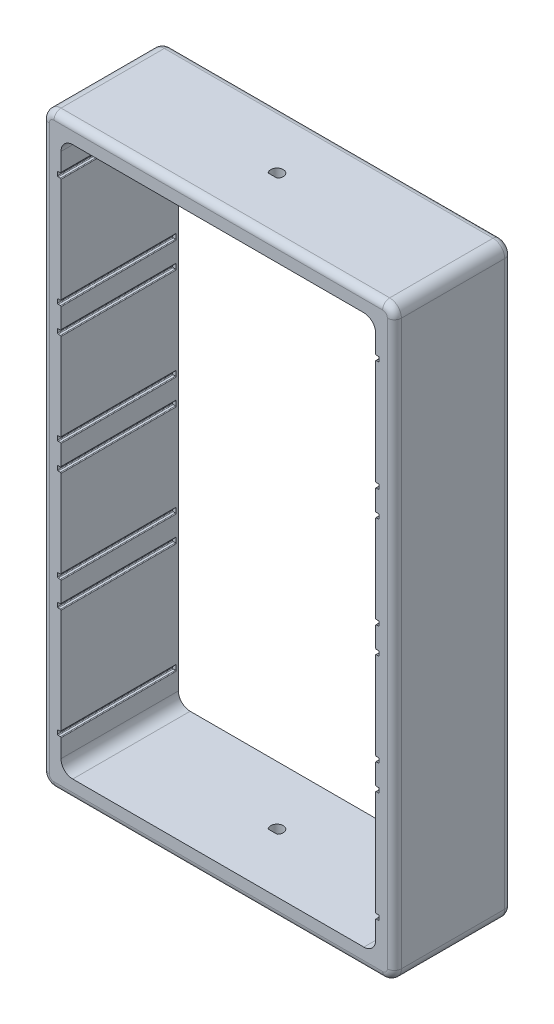
SolidWorks part; units mm, degrees
other "Markup1"
sketch "Sketch8" plane through (101.6, 152.4, 25.4) normal (0.0906, 0.2617, 0.9609) x (0.9959, -0.0171, -0.0892)
ref_plane "Front Plane" through (0, 0, 0) normal (0, 0, 1) x (1, 0, 0)
ref_plane "Top Plane" through (0, 0, 0) normal (0, 1, 0) x (1, 0, 0)
ref_plane "Right Plane" through (0, 0, 0) normal (1, 0, 0) x (0, 0, -1)
sketch "Sketch1" plane through (0, 0, 0) normal (0, 0, 1) x (1, 0, 0)
  line L1 (0, 0) -> (150, 0)
  line L2 (0, 0) -> (0, 250)
  line L3 (0, 250) -> (150, 250)
  line L4 (150, 0) -> (150, 250)
  dimension "D1" = 250
  dimension "D2" = 150
extrude "Boss-Extrude1" add sketch "Sketch1" along normal mid plane 50
sketch "Sketch2" plane through (0, 0, 25) normal (0, 0, 1) x (1, 0, 0)
  line L7 (150, 0) -> (150, 250) construction
  line L8 (8, 242) -> (142, 242)
  line L9 (8, 242) -> (8, 8)
  line L10 (8, 8) -> (142, 8)
  line L11 (142, 242) -> (142, 8)
  line L12 (8, 242) -> (142, 8) construction
  line L13 (8, 8) -> (142, 242) construction
  line L14 (150, 250) -> (0, 250) construction
  line L16 (0, 250) -> (0, 0) construction
  point P0 (75, 125)
  point P9 (150, 125)
  point P12 (75, 250)
  dimension "D1" = 8
  dimension "D2" = 8
extrude "Cut-Extrude1" cut sketch "Sketch2" against normal through all
sketch "Sketch3" plane through (0, 250, 0) normal (0, 1, 0) x (1, 0, 0)
  line L0 (150, -25) -> (150, 25) construction
  line L1 (150, 25) -> (0, 25) construction
  line L5 (73.09, -1.837) -> (76.91, -1.837)
  arc A0 (76.91, -1.837) -> (73.09, -1.837) centre (75, 0) ccw
  point P5 (150, 0)
  point P9 (75, 25)
  point P12 (75, 2.65)
  dimension "D1" = 5.3
  dimension "D2" = 3.82
extrude "Cut-Extrude2" cut sketch "Sketch3" against normal through all
sketch "Sketch7" plane through (0, 0, 25) normal (0, 0, 1) x (1, 0, 0)
  line L0 (6.5, 182) -> (8, 182)
  line L1 (142, 242) -> (8, 242) construction
  line L2 (8, 242) -> (8, 8) construction
  line L3 (6.5, 229) -> (8, 229)
  line L4 (6.5, 229) -> (6.5, 227)
  line L5 (6.5, 227) -> (8, 227)
  line L6 (8, 229) -> (8, 227)
  line L7 (6.5, 182) -> (6.5, 180)
  line L8 (6.5, 180) -> (8, 180)
  line L9 (8, 182) -> (8, 180)
  line L10 (6.5, 171) -> (8, 171)
  line L11 (6.5, 171) -> (6.5, 169)
  line L12 (6.5, 169) -> (8, 169)
  line L13 (8, 171) -> (8, 169)
  line L14 (142, 125) -> (8, 125) construction
  line L15 (142, 8) -> (142, 242) construction
  line L16 (6.5, 81) -> (8, 81)
  line L17 (6.5, 79) -> (6.5, 81)
  line L18 (6.5, 21) -> (6.5, 23)
  line L19 (6.5, 21) -> (8, 21)
  line L20 (8, 79) -> (8, 81)
  line L21 (6.5, 79) -> (8, 79)
  line L22 (8, 68) -> (8, 70)
  line L23 (6.5, 70) -> (8, 70)
  line L24 (6.5, 68) -> (6.5, 70)
  line L25 (8, 21) -> (8, 23)
  line L26 (6.5, 23) -> (8, 23)
  line L27 (6.5, 68) -> (8, 68)
  line L28 (6.5, 131.5) -> (8, 131.5)
  line L29 (6.5, 131.5) -> (6.5, 129.5)
  line L30 (6.5, 129.5) -> (8, 129.5)
  line L31 (8, 131.5) -> (8, 129.5)
  line L32 (6.5, 120.5) -> (8, 120.5)
  line L33 (6.5, 120.5) -> (6.5, 118.5)
  line L34 (6.5, 118.5) -> (8, 118.5)
  line L35 (8, 120.5) -> (8, 118.5)
  line L36 (6.5, 129.5) -> (6.5, 120.5) construction
  line L37 (75, 242) -> (75, 8) construction
  line L38 (8, 8) -> (142, 8) construction
  line L39 (143.5, 129.5) -> (143.5, 120.5) construction
  line L40 (142, 120.5) -> (142, 118.5)
  line L41 (143.5, 118.5) -> (142, 118.5)
  line L42 (143.5, 120.5) -> (143.5, 118.5)
  line L43 (143.5, 120.5) -> (142, 120.5)
  line L44 (142, 131.5) -> (142, 129.5)
  line L45 (143.5, 129.5) -> (142, 129.5)
  line L46 (143.5, 131.5) -> (143.5, 129.5)
  line L47 (143.5, 131.5) -> (142, 131.5)
  line L48 (143.5, 68) -> (142, 68)
  line L49 (143.5, 23) -> (142, 23)
  line L50 (142, 21) -> (142, 23)
  line L51 (143.5, 68) -> (143.5, 70)
  line L52 (143.5, 70) -> (142, 70)
  line L53 (142, 68) -> (142, 70)
  line L54 (143.5, 79) -> (142, 79)
  line L55 (142, 79) -> (142, 81)
  line L56 (143.5, 21) -> (142, 21)
  line L57 (143.5, 21) -> (143.5, 23)
  line L58 (143.5, 79) -> (143.5, 81)
  line L59 (143.5, 81) -> (142, 81)
  line L60 (142, 171) -> (142, 169)
  line L61 (143.5, 169) -> (142, 169)
  line L62 (143.5, 171) -> (143.5, 169)
  line L63 (143.5, 171) -> (142, 171)
  line L64 (142, 182) -> (142, 180)
  line L65 (143.5, 180) -> (142, 180)
  line L66 (143.5, 182) -> (143.5, 180)
  line L67 (142, 229) -> (142, 227)
  line L68 (143.5, 227) -> (142, 227)
  line L69 (143.5, 229) -> (143.5, 227)
  line L70 (143.5, 229) -> (142, 229)
  line L71 (143.5, 182) -> (142, 182)
  point P41 (6.5, 125)
  dimension "D1" = 1.5
  dimension "D2" = 2
  dimension "D3" = 15
  dimension "D4" = 1.5
  dimension "D5" = 2
  dimension "D6" = 60
  dimension "D7" = 1.5
  dimension "D8" = 2
  dimension "D9" = 9
  dimension "D10" = 1.5
  dimension "D11" = 2
  dimension "D12" = 1.5
  dimension "D13" = 2
  dimension "D14" = 9
extrude "Cut-Extrude5" cut sketch "Sketch7" against normal blind 49
fillet "Fillet1" radius 5 8 edges at (150, 0, 0) (0, 0, 0) (150, 250, 0) (0, 250, 0) (142, 242, 0) (8, 242, 0) (142, 8, 0) (8, 8, 0)
fillet "Fillet2" radius 3 16 edges at (1.4645, 248.5355, -25) (75, 250, -25) (148.5355, 248.5355, -25) (150, 125, -25) (148.5355, 1.4645, -25) (75, 0, -25) (1.4645, 1.4645, -25) (1.4645, 248.5355, 25) (75, 250, 25) (148.5355, 248.5355, 25) (150, 125, 25) (148.5355, 1.4645, 25) (75, 0, 25) (1.4645, 1.4645, 25) (0, 125, -25) (0, 125, 25)
fillet "Fillet3" radius 0.3 64 edges at (8, 229, 0.5) (8, 227, 0.5) (6.5, 227, 0.5) (6.5, 229, 0.5) (8, 23, 0.5) (6.5, 23, 0.5) (6.5, 21, 0.5) (8, 21, 0.5) (142, 21, 0.5) (143.5, 21, 0.5) (143.5, 23, 0.5) (142, 23, 0.5) (142, 68, 0.5) (143.5, 68, 0.5) (143.5, 70, 0.5) (142, 70, 0.5) (142, 79, 0.5) (143.5, 79, 0.5) (143.5, 81, 0.5) (142, 81, 0.5) (142, 118.5, 0.5) (143.5, 118.5, 0.5) (143.5, 120.5, 0.5) (142, 120.5, 0.5) (142, 129.5, 0.5) (143.5, 129.5, 0.5) (143.5, 131.5, 0.5) (142, 131.5, 0.5) (142, 169, 0.5) (143.5, 169, 0.5) (143.5, 171, 0.5) (142, 171, 0.5) (142, 180, 0.5) (143.5, 180, 0.5) (143.5, 182, 0.5) (142, 182, 0.5) (142, 227, 0.5) (143.5, 227, 0.5) (143.5, 229, 0.5) (142, 229, 0.5) (8, 182, 0.5) (6.5, 182, 0.5) (8, 180, 0.5) (8, 171, 0.5) (6.5, 171, 0.5) (6.5, 169, 0.5) (8, 169, 0.5) (8, 131.5, 0.5) (6.5, 131.5, 0.5) (6.5, 129.5, 0.5) (8, 129.5, 0.5) (8, 120.5, 0.5) (6.5, 120.5, 0.5) (6.5, 118.5, 0.5) (8, 118.5, 0.5) (8, 81, 0.5) (6.5, 81, 0.5) (6.5, 79, 0.5) (8, 79, 0.5) (8, 70, 0.5) (6.5, 70, 0.5) (6.5, 68, 0.5) (8, 68, 0.5) (6.5, 180, 0.5)
